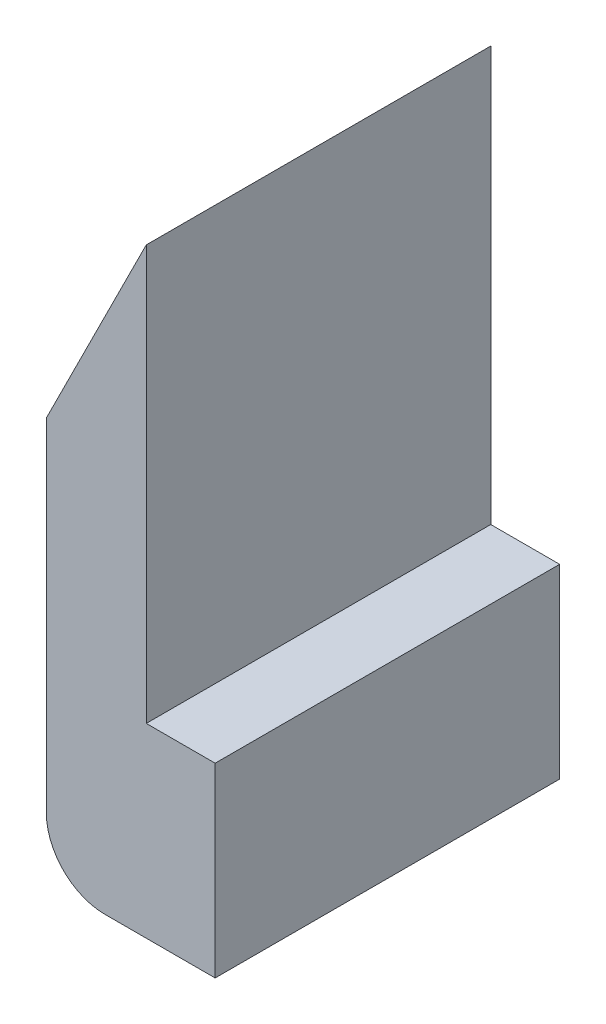
SolidWorks part; units mm, degrees
ref_plane "Front Plane" through (0, 0, 0) normal (0, 0, 1) x (1, 0, 0)
ref_plane "Top Plane" through (0, 0, 0) normal (0, 1, 0) x (1, 0, 0)
ref_plane "Right Plane" through (0, 0, 0) normal (1, 0, 0) x (0, 0, -1)
sketch "Sketch1" plane through (0, 0, 0) normal (0, 0, 1) x (1, 0, 0)
  line L0 (2, -6) -> (0, -6) construction
  line L1 (2, -6) -> (2, 0) construction
  line L2 (2, 0) -> (0, 0) construction
  line L3 (0, -6) -> (-1.5, -6) construction
  line L4 (0, 0) -> (0, 13) construction
  line L5 (0, 13) -> (-3.5, 6) construction
  line L6 (-3.5, -4) -> (-3.5, 6) construction
  line L7 (-0.3, 11.7292) -> (-3.2, 5.9292)
  line L8 (-3.2, -4) -> (-3.2, 5.9292)
  line L9 (0, -5.7) -> (-1.5, -5.7)
  line L10 (1.7, -5.7) -> (0, -5.7)
  line L11 (1.7, -5.7) -> (1.7, -0.3)
  line L12 (1.7, -0.3) -> (-0.3, -0.3)
  line L13 (-0.3, -0.3) -> (-0.3, 11.7292)
  arc A0 (-1.5, -6) -> (-3.5, -4) centre (-1.5, -4) cw construction
  arc A1 (-1.5, -5.7) -> (-3.2, -4) centre (-1.5, -4) cw
  point P9 (0, 0)
  point P11 (-7.6987, -8.8926)
  point P12 (0, 0)
  point P13 (0, -9.0205)
  point P14 (0, 0)
  point P15 (0, 0)
  dimension "D4" = 2
  dimension "D1" = 6
  dimension "D2" = 3.5
  dimension "D3" = 2
  dimension "D5" = 13
  dimension "D6" = 10
  dimension "D7" = 0.3
extrude "Boss-Extrude1" add sketch "Sketch1" along normal blind 10
